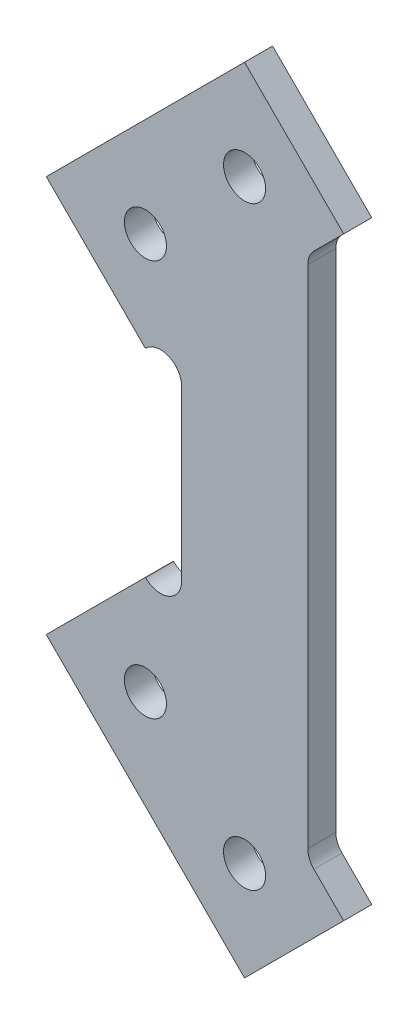
SolidWorks part; units mm, degrees
ref_plane "Front Plane" through (0, 0, 0) normal (0, 0, 1) x (1, 0, 0)
ref_plane "Top Plane" through (0, 0, 0) normal (0, 1, 0) x (1, 0, 0)
ref_plane "Right Plane" through (0, 0, 0) normal (1, 0, 0) x (0, 0, -1)
sketch "Sketch1" plane through (0, 0, 0) normal (0, 0, 1) x (1, 0, 0)
  line L0 (-14.163, -28.2843) -> (-0.0208, -42.4264) construction
  line L1 (-14.163, 28.2843) -> (-0.0208, 42.4264) construction
  line L2 (-14.163, 14.1421) -> (-14.1213, 14.1838)
  line L3 (14.1213, 42.4264) -> (-0.0208, 56.5685)
  line L4 (-0.0208, 56.5685) -> (-28.3051, 28.2843)
  line L5 (-28.3051, 28.2843) -> (-14.163, 14.1421)
  line L6 (-14.163, -14.1421) -> (-14.1213, -14.1838)
  line L7 (14.1213, -42.4264) -> (-0.0208, -56.5685)
  line L8 (-0.0208, -56.5685) -> (-28.3051, -28.2843)
  line L9 (-28.3051, -28.2843) -> (-14.163, -14.1421)
  line L10 (-0.0208, 42.4264) -> (7.0503, 49.4975) construction
  line L11 (-0.0208, -42.4264) -> (7.0503, -49.4975) construction
  line L12 (0, 28.3051) -> (0, -28.3051) construction
  line L13 (-9, 12.0624) -> (-9, -12.0624)
  line L14 (9, 36.0624) -> (9, -36.0624)
  line L15 (9.8787, 38.1838) -> (14.1213, 42.4264)
  line L16 (9.8787, -38.1838) -> (14.1213, -42.4264)
  line L17 (-9, -19.3051) -> (9, -37.3051) construction
  line L18 (-9, 19.3051) -> (9, 37.3051) construction
  circle A0 centre (-0.0208, 42.4264) radius 3
  circle A1 centre (-14.163, 28.2843) radius 3
  circle A2 centre (-14.163, -28.2843) radius 3
  circle A3 centre (-0.0208, -42.4264) radius 3
  arc A4 (9, -36.0624) -> (9.8787, -38.1838) centre (12, -36.0624) ccw
  arc A5 (9.8787, 38.1838) -> (9, 36.0624) centre (12, 36.0624) ccw
  arc A6 (-9, 12.0624) -> (-14.1213, 14.1838) centre (-12, 12.0624) ccw
  arc A7 (-9, -12.0624) -> (-14.1213, -14.1838) centre (-12, -12.0624) cw
  dimension "D8" = 6
  dimension "D9" = 3
  dimension "D1" = 20
  dimension "D2" = 10
  dimension "D3" = 20
  dimension "D4" = 40
  dimension "D5" = 70
  dimension "D6" = 45
  dimension "D7" = 18
  dimension "D10" = 6
extrude "Boss-Extrude1" add sketch "Sketch1" along normal blind 4
